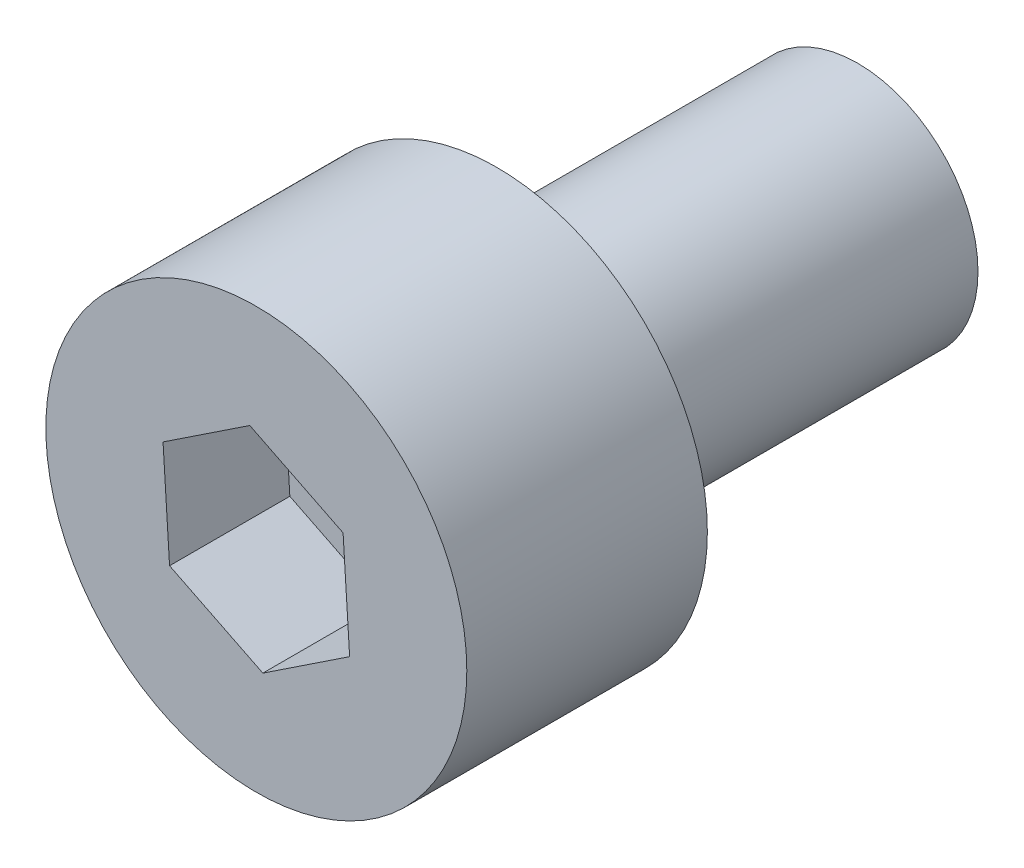
SolidWorks part; units mm, degrees
ref_plane "前视基准面" through (0, 0, 0) normal (0, 0, 1) x (1, 0, 0)
ref_plane "上视基准面" through (0, 0, 0) normal (0, 1, 0) x (1, 0, 0)
ref_plane "右视基准面" through (0, 0, 0) normal (1, 0, 0) x (0, 0, -1)
sketch "草图1" plane through (0, 0, 0) normal (0, 0, 1) x (1, 0, 0)
  circle A0 centre (0, 0) radius 3.5
  dimension "D1" = 7
extrude "凸台-拉伸1" add sketch "草图1" along normal blind 4
sketch "草图2" plane through (0, 0, 4) normal (0, 0, 1) x (1, 0, 0)
  line L1 (1.5513, -0.7703) -> (1.4428, 0.9583)
  line L2 (1.4428, 0.9583) -> (-0.1086, 1.7286)
  line L3 (-0.1086, 1.7286) -> (-1.5513, 0.7703)
  line L4 (-1.5513, 0.7703) -> (-1.4428, -0.9583)
  line L5 (-1.4428, -0.9583) -> (0.1086, -1.7286)
  line L6 (0.1086, -1.7286) -> (1.5513, -0.7703)
  circle A0 centre (0, 0) radius 1.5 construction
  dimension "D1" = 3
extrude "切除-拉伸1" cut sketch "草图2" against normal blind 2
sketch "草图3" plane through (0, 0, 0) normal (0, 0, -1) x (-1, 0, 0)
  circle A0 centre (0, 0) radius 2
  circle A1 centre (0, 0) radius 3.5
  circle A2 centre (0, 0) radius 3.5
  dimension "D2" = 4
  dimension "D1" = 0
extrude "凸台-拉伸2" add sketch "草图3" along normal blind 6 contours A0
